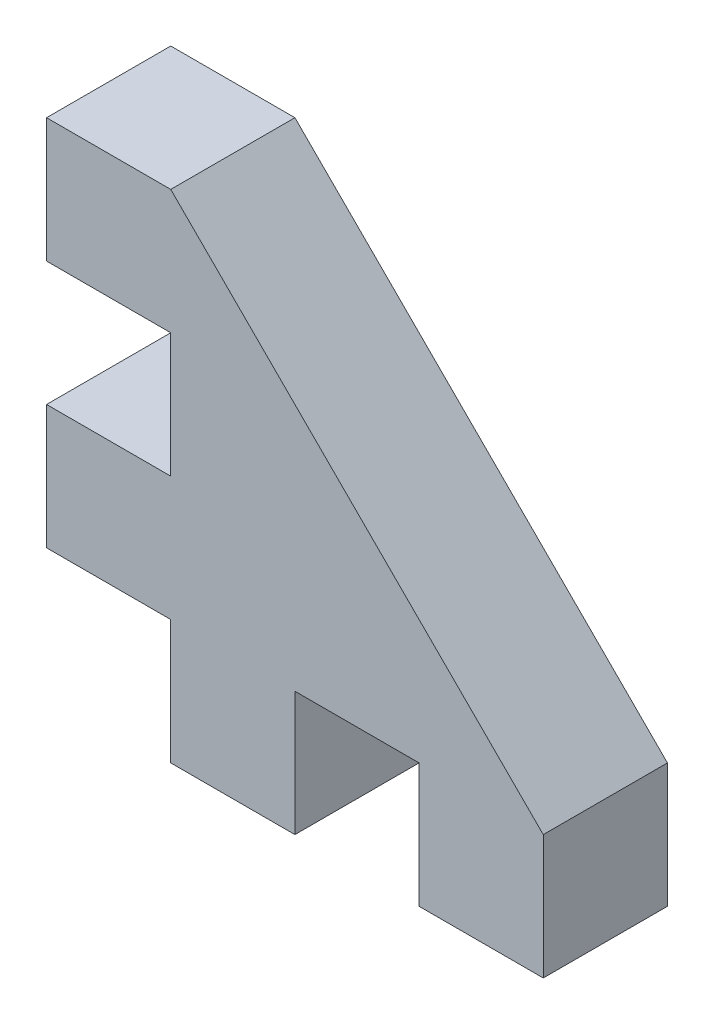
SolidWorks part; units mm, degrees
ref_plane "Plan de face" through (0, 0, 0) normal (0, 0, 1) x (1, 0, 0)
ref_plane "Plan de dessus" through (0, 0, 0) normal (0, 1, 0) x (1, 0, 0)
ref_plane "Plan de droite" through (0, 0, 0) normal (1, 0, 0) x (0, 0, -1)
sketch "Esquisse1" plane through (0, 0, 0) normal (0, 0, 1) x (1, 0, 0)
  line L1 (-43.243, 14.2635) -> (-23.243, 14.2635)
  line L2 (-43.243, 14.2635) -> (-43.243, -5.7365)
  line L3 (-43.243, -5.7365) -> (-23.243, -5.7365)
  line L4 (-23.243, 14.2635) -> (-23.243, -5.7365)
extrude "Boss.-Extru.1" add sketch "Esquisse1" along normal blind 5
sketch "Esquisse2" plane through (0, 0, 5) normal (0, 0, 1) x (1, 0, 0)
  line L0 (-33.243, -5.7365) -> (-28.243, -5.7365)
  line L1 (-43.243, -5.7365) -> (-38.243, -5.7365)
  line L2 (-43.243, -5.7365) -> (-43.243, -0.7365)
  line L3 (-43.243, -0.7365) -> (-38.243, -0.7365)
  line L4 (-38.243, -5.7365) -> (-38.243, -0.7365)
  line L5 (-33.243, -5.7365) -> (-33.243, -0.7365)
  line L6 (-33.243, -0.7365) -> (-28.243, -0.7365)
  line L7 (-28.243, -5.7365) -> (-28.243, -0.7365)
  line L8 (-43.243, 4.2635) -> (-38.243, 4.2635)
  line L9 (-43.243, 4.2635) -> (-43.243, 9.2635)
  line L10 (-43.243, 9.2635) -> (-38.243, 9.2635)
  line L11 (-38.243, 4.2635) -> (-38.243, 9.2635)
  line L12 (-23.243, 14.2635) -> (-43.243, 14.2635) construction
  line L13 (-23.243, 14.2635) -> (-38.243, 14.2635)
  line L14 (-38.243, 14.2635) -> (-23.243, -0.7365)
  line L15 (-23.243, -5.7365) -> (-23.243, 14.2635) construction
  line L16 (-23.243, -0.7365) -> (-23.243, 14.2635)
  dimension "D1" = 2
  dimension "D2" = 2
extrude "Enlèv. mat.-Extru.1" cut sketch "Esquisse2" along direction (0, 0, 1) on the side against the normal blind 5
